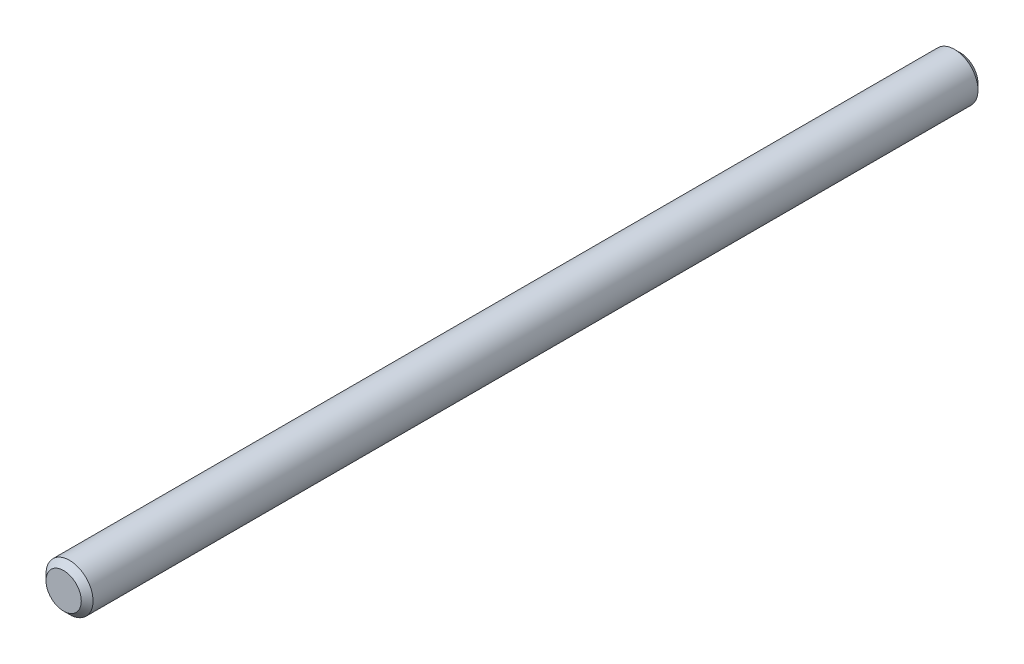
SolidWorks part; units mm, degrees
ref_plane "Front Plane" through (0, 0, 0) normal (0, 0, 1) x (1, 0, 0)
ref_plane "Top Plane" through (0, 0, 0) normal (0, 1, 0) x (1, 0, 0)
ref_plane "Right Plane" through (0, 0, 0) normal (1, 0, 0) x (0, 0, -1)
sketch "Sketch1" plane through (0, 0, 0) normal (0, 1, 0) x (1, 0, 0)
  line L0 (1.1862, 0) -> (0, 0)
  line L1 (0, 0) -> (0, -60.325)
  line L2 (0, -60.325) -> (1.1862, -60.325)
  line L3 (1.1862, -60.325) -> (1.5824, -59.9288)
  line L4 (1.5824, -59.9288) -> (1.5824, -0.3962)
  line L5 (1.5824, -0.3962) -> (1.1862, 0)
  line L6 (0, 0) -> (0, -60.325) construction
revolve "Revolve1" add sketch "Sketch1" angle 360 about L6
